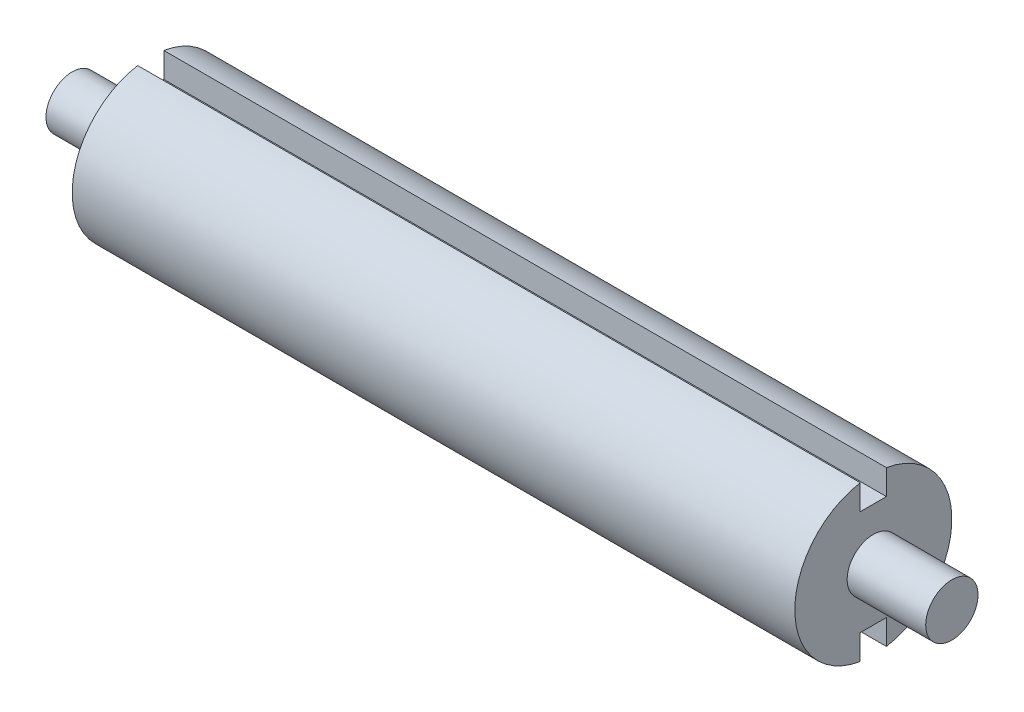
SolidWorks part; units mm, degrees
material "6061 Alloy"
ref_plane "Front Plane" through (0, 0, 0) normal (0, 0, 1) x (1, 0, 0)
ref_plane "Top Plane" through (0, 0, 0) normal (0, 1, 0) x (1, 0, 0)
ref_plane "Right Plane" through (0, 0, 0) normal (1, 0, 0) x (0, 0, -1)
sketch "Sketch1" plane through (0, 0, 0) normal (0, 1, 0) x (1, 0, 0)
  line L0 (-106.68, 0) -> (106.68, 0)
  line L1 (-106.68, 0) -> (-106.68, 6.35)
  line L2 (-106.68, 6.35) -> (-87.63, 6.35)
  line L3 (-87.63, 6.35) -> (-87.63, 19.05)
  line L4 (-87.63, 19.05) -> (87.63, 19.05)
  line L5 (87.63, 19.05) -> (87.63, 6.35)
  line L6 (87.63, 6.35) -> (106.68, 6.35)
  line L7 (106.68, 6.35) -> (106.68, 0)
  dimension "D1" = 175.26
  dimension "D2" = 19.05
  dimension "D3" = 6.35
  dimension "D4" = 19.05
revolve "Revolve1" add sketch "Sketch1" angle 360 about L0
sketch "Sketch2" plane through (87.63, 0, 0) normal (1, 0, 0) x (0, 0, -1)
  line L0 (-6.35, 0) -> (6.35, 0) construction
  line L1 (-3.175, 12.7) -> (3.175, 12.7)
  line L2 (-3.175, 12.7) -> (-3.175, 19.05)
  line L3 (-3.175, 19.05) -> (3.175, 19.05)
  line L4 (3.175, 12.7) -> (3.175, 19.05)
  line L5 (-3.175, 12.7) -> (3.175, 19.05) construction
  line L6 (-3.175, 19.05) -> (3.175, 12.7) construction
  line L7 (-3.175, -19.05) -> (3.175, -12.7) construction
  line L8 (-3.175, -12.7) -> (3.175, -19.05) construction
  line L9 (3.175, -12.7) -> (3.175, -19.05)
  line L10 (-3.175, -19.05) -> (3.175, -19.05)
  line L11 (-3.175, -12.7) -> (-3.175, -19.05)
  line L12 (-3.175, -12.7) -> (3.175, -12.7)
  circle A0 centre (0, 0) radius 19.05 construction
  circle A1 centre (0, 0) radius 6.35 construction
  circle A2 centre (0, 0) radius 6.35 construction
  point P0 (0, 15.875)
  point P19 (0, -15.875)
  dimension "D1" = 6.35
  dimension "D2" = 6.35
extrude "Cut-Extrude1" cut sketch "Sketch2" against normal through all
